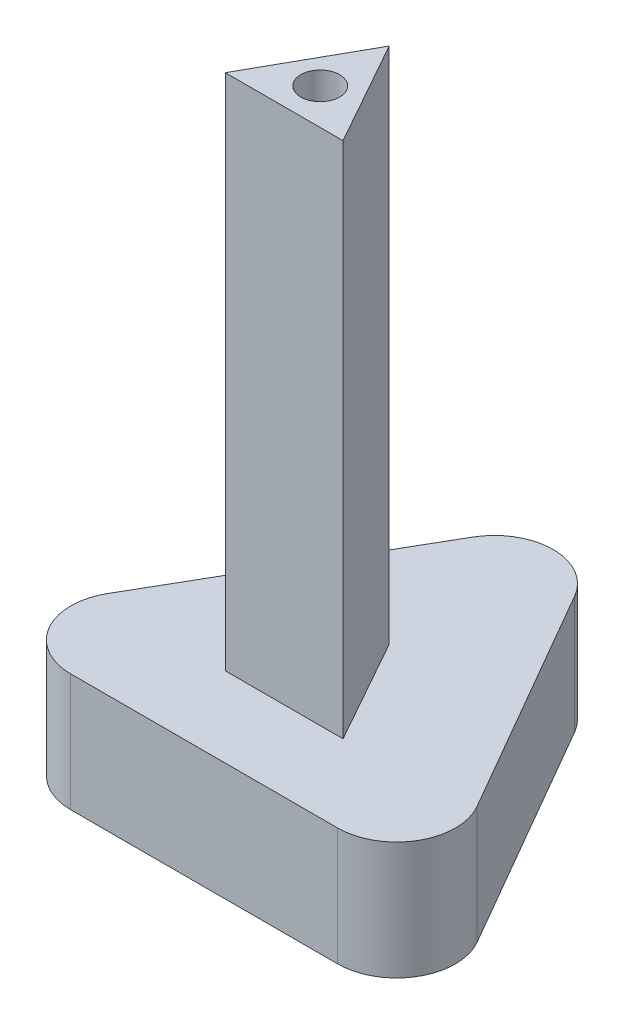
SolidWorks part; units mm, degrees
ref_plane "前视基准面" through (0, 0, 0) normal (0, 0, 1) x (1, 0, 0)
ref_plane "上视基准面" through (0, 0, 0) normal (0, 1, 0) x (1, 0, 0)
ref_plane "右视基准面" through (0, 0, 0) normal (1, 0, 0) x (0, 0, -1)
sketch "草图1" plane through (0, 0, 0) normal (0, 1, 0) x (1, 0, 0)
  line L0 (-17.1131, 2.8406) -> (-37.1131, -31.8004)
  line L1 (-37.1131, -31.8004) -> (2.8869, -31.8004)
  line L2 (-17.1131, 2.8406) -> (2.8869, -31.8004)
extrude "凸台-拉伸1" add sketch "草图1" along normal blind 10
fillet "圆角1" radius 5 3 edges at (2.8869, 5, 31.8004) (-37.1131, 5, 31.8004) (-17.1131, 5, -2.8406)
sketch "草图2" plane through (0, 10, 0) normal (0, 1, 0) x (1, 0, 0)
  line L0 (-17.1131, -16.0862) -> (-12.1131, -25.0113)
  line L1 (-12.1131, -25.0113) -> (-22.1131, -25.0113)
  line L2 (-22.1131, -25.0113) -> (-17.1131, -16.0862)
  line L3 (-17.1131, -2.1594) -> (-17.1131, -25.0113)
  arc A0 (-12.7829, -4.6594) -> (-21.4432, -4.6594) centre (-17.1131, -7.1594) ccw construction
extrude "凸台-拉伸2" add sketch "草图2" along normal blind 44 contours L0 L1 L2
sketch "草图3" plane through (0, 54, 0) normal (0, 1, 0) x (1, 0, 0)
  line L0 (-17.1131, -16.0862) -> (-17.1131, -21.9493)
  line L1 (-17.1131, -21.9493) -> (-22.1131, -25.0113)
  point P3 (-17.1131, -21.9493)
hole_wizard "M4 螺纹孔1" positions "草图4" profile "草图5" tap size "M4" standard "GB"
sketch "草图4" plane through (0, 54, 0) normal (0, 1, 0) x (1, 0, 0)
  point P0 (-17.1131, -21.9493)
sketch "草图5" plane through (-17.1131, 54, 21.9493) normal (1, 0, 0) x (0, 0, 1)
  line L0 (0, 0) -> (0, 11.0914)
  line L1 (0, 11.0914) -> (1.65, 10.1)
  line L2 (1.65, 10.1) -> (1.65, 0)
  line L5 (1.65, 0) -> (0, 0)
  line L10 (0, 11.0914) -> (-1.65, 10.1) construction
  line L11 (0, -6.35) -> (0, 107.95) construction
  dimension "螺纹孔钻头直径" = 3.3
  dimension "螺纹孔钻头深度" = 10.1
  dimension "导头角度" = 118
cosmetic thread "孔螺蚊线1" parameters "D1"=8, "D2"=4
